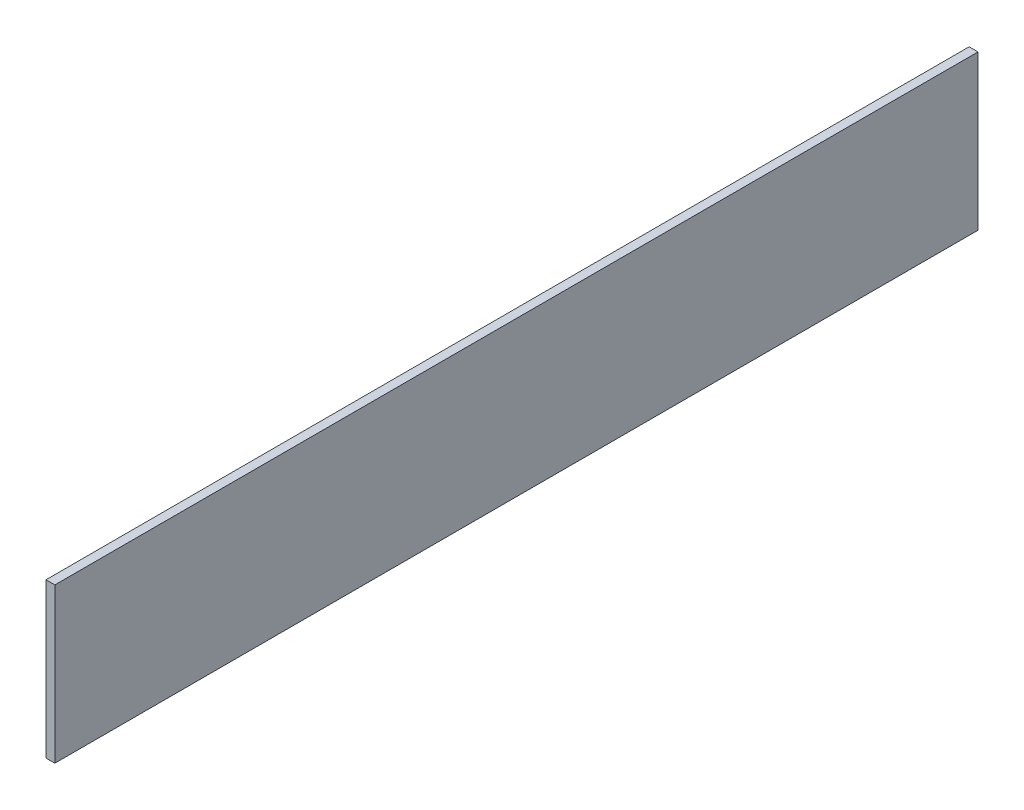
SolidWorks part; units mm, degrees
ref_plane "Front Plane" through (0, 0, 0) normal (1, 0, 0) x (0, 1, 0)
ref_plane "Top Plane" through (0, 0, 0) normal (0, 0, 1) x (0, 1, 0)
ref_plane "Right Plane" through (0, 0, 0) normal (0, 1, 0) x (-1, 0, 0)
sketch "Sketch1" plane through (0, 0, 0) normal (1, 0, 0) x (0, 1, 0)
  line L0 (-35, 127.5) -> (-35, -127.5) construction
  line L1 (0, 100) -> (-35, 100)
  line L2 (0, 100) -> (0, -100)
  line L3 (0, -100) -> (-35, -100)
  line L4 (-35, 100) -> (-35, -100)
  line L5 (0, -100) -> (-35, -100) construction
extrude "Boss-Extrude1" add sketch "Sketch1" along normal mid plane 5
sketch "Sketch2" plane through (0, 0, 0) normal (1, 0, 0) x (0, 0, -1)
  line L1 (-130, -41) -> (130, -41)
  line L2 (-130, -41) -> (-130, 2.5)
  line L3 (-130, 2.5) -> (130, 2.5)
  line L4 (130, -41) -> (130, 2.5)
extrude "Boss-Extrude2" add sketch "Sketch2" along normal blind 2.5
